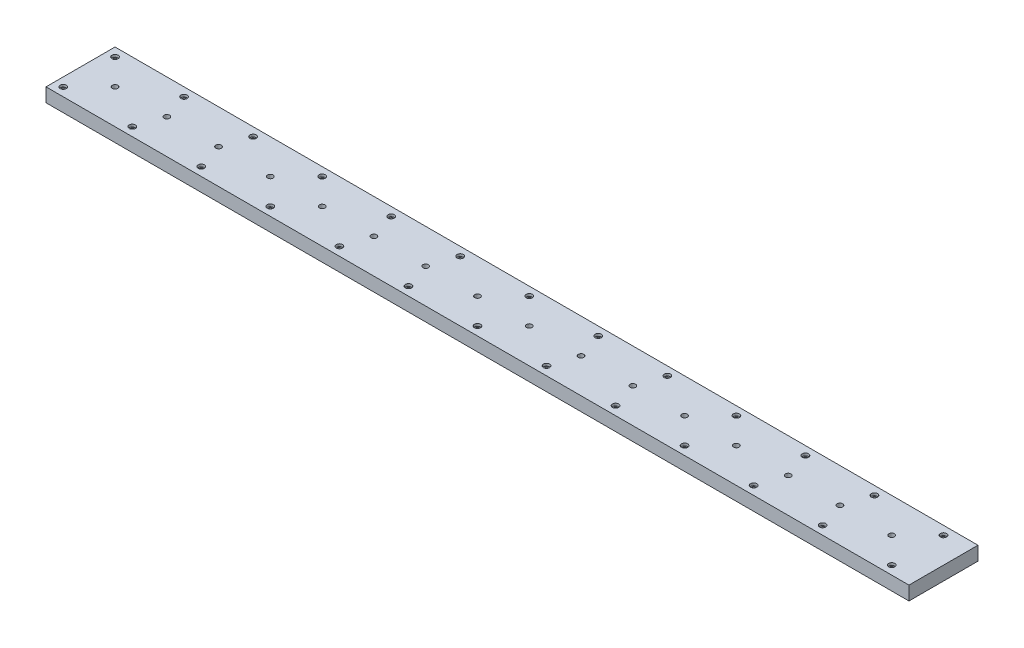
SolidWorks part; units mm, degrees
material "Liga 6061"
ref_plane "Plano frontal" through (0, 0, 0) normal (0, 0, 1) x (1, 0, 0)
ref_plane "Plano superior" through (0, 0, 0) normal (0, 1, 0) x (1, 0, 0)
ref_plane "Plano direito" through (0, 0, 0) normal (1, 0, 0) x (0, 0, -1)
sketch "Esboço1" plane through (0, 0, 0) normal (0, 1, 0) x (1, 0, 0)
  line L1 (-1250, -100) -> (1250, -100)
  line L2 (-1250, -100) -> (-1250, 100)
  line L3 (-1250, 100) -> (1250, 100)
  line L4 (1250, -100) -> (1250, 100)
  line L5 (-1250, -100) -> (1250, 100) construction
  line L6 (-1250, 100) -> (1250, -100) construction
  point P0 (0, 0)
  dimension "D1" = 2500
  dimension "D2" = 200
extrude "Ressalto-extrusão1" add sketch "Esboço1" along normal blind 40
hole_wizard "Rebaixo para parafuso Allen sextavado de M101" positions "Esboço3" profile "Esboço2" counterbore size "M10" standard "DIN" end condition up to next
sketch "Esboço3" plane through (0, 40, 0) normal (0, 1, 0) x (1, 0, 0)
  line L0 (-1250, 100) -> (-1250, -100) construction
  line L1 (1250, 100) -> (-1250, 100) construction
  point P0 (-1225, 75)
  point P12 (-1025, 75)
  point P13 (-825, 75)
  point P14 (-625, 75)
  point P15 (-425, 75)
  point P16 (-225, 75)
  point P17 (-25, 75)
  point P18 (175, 75)
  point P19 (375, 75)
  point P20 (575, 75)
  point P21 (-1025, -75)
  point P22 (-825, -75)
  point P23 (-625, -75)
  point P24 (-425, -75)
  point P25 (-225, -75)
  point P26 (-25, -75)
  point P27 (175, -75)
  point P28 (375, -75)
  point P29 (575, -75)
  point P30 (-1225, -75)
  point P31 (775, 75)
  point P32 (775, -75)
  point P33 (975, 75)
  point P34 (1175, 75)
  point P35 (975, -75)
  point P36 (1175, -75)
  dimension "D1" = 25
  dimension "D2" = 25
  dimension "D3" = 13
  dimension "D4" = 2
sketch "Esboço2" plane through (-1225, 40, -75) normal (1, 0, 0) x (0, 0, 1)
  line L0 (0, 0) -> (0, 40)
  line L1 (0, 40) -> (5.5, 40)
  line L3 (5.5, 40) -> (5.5, 7.1)
  line L4 (5.5, 7.1) -> (9, 7.1)
  line L5 (9, 7.1) -> (9, 0)
  line L7 (9, 0) -> (0, 0)
  line L11 (0, -6.35) -> (0, 107.95) construction
  dimension "Thru Hole Dia." = 11
  dimension "Thru Hole Depth" = 40
  dimension "C'Bore Dia." = 18
  dimension "C'Bore Depth" = 7.1
hole_wizard "Furo roscado de M18x2.0" positions "Esboço7" profile "Esboço6" tap size "M18x2.0" standard "Ansi Metric" end condition up to next
sketch "Esboço7" plane through (0, 40, 0) normal (0, 1, 0) x (1, 0, 0)
  line L0 (-1250, 100) -> (-1250, -100) construction
  line L1 (-1150, 0) -> (-1250, 0) construction
  point P0 (-1150, 0)
  point P5 (-1250, 0)
  point P72 (-1000, 0)
  point P73 (-850, 0)
  point P74 (-700, 0)
  point P75 (-550, 0)
  point P76 (-400, 0)
  point P77 (-250, 0)
  point P78 (-100, 0)
  point P79 (50, 0)
  point P80 (200, 0)
  point P81 (350, 0)
  point P82 (500, 0)
  point P83 (650, 0)
  point P84 (800, 0)
  point P85 (950, 0)
  point P86 (1100, 0)
  dimension "D2" = 100
  dimension "D1" = 16
sketch "Esboço6" plane through (-1150, 40, 0) normal (1, 0, 0) x (0, 0, 1)
  line L0 (0, 0) -> (0, 40)
  line L1 (0, 40) -> (8, 40)
  line L2 (8, 40) -> (8, 0)
  line L5 (8, 0) -> (0, 0)
  line L11 (0, -6.35) -> (0, 107.95) construction
  dimension "Thru Tap Drill Dia." = 16
  dimension "Thru Tap Drill Depth" = 40
cosmetic thread "Rosca de furo5" parameters "D2"=16
cosmetic thread "Rosca de furo6" parameters "D2"=16
cosmetic thread "Rosca de furo7" parameters "D2"=16
cosmetic thread "Rosca de furo8" parameters "D2"=16
cosmetic thread "Rosca de furo9" parameters "D2"=16
cosmetic thread "Rosca de furo10" parameters "D2"=16
cosmetic thread "Rosca de furo11" parameters "D2"=16
cosmetic thread "Rosca de furo12" parameters "D2"=16
cosmetic thread "Rosca de furo13" parameters "D2"=16
cosmetic thread "Rosca de furo14" parameters "D2"=16
cosmetic thread "Rosca de furo15" parameters "D2"=16
cosmetic thread "Rosca de furo16" parameters "D2"=16
cosmetic thread "Rosca de furo17" parameters "D2"=16
cosmetic thread "Rosca de furo18" parameters "D2"=16
cosmetic thread "Rosca de furo37" parameters "D2"=16
cosmetic thread "Rosca de furo38" parameters "D2"=16
hole_wizard "Furo roscado de M16x2.0" [suppressed] positions "Esboço9" profile "Esboço8" tap size "M16x2.0" standard "Ansi Metric"
sketch "Esboço9" plane through (0, 40, 0) normal (0, 1, 0) x (1, 0, 0)
  line L0 (-1020, 0) -> (-1050, 0) construction
  line L1 (-1050, 100) -> (-1050, -100) construction
  line L2 (1020, 0) -> (1050, 0) construction
  line L3 (1050, -100) -> (1050, 100) construction
  point P0 (-1020, 0)
  point P13 (-900, 0)
  point P14 (-780, 0)
  point P15 (-660, 0)
  point P16 (-540, 0)
  point P17 (-420, 0)
  point P18 (-300, 0)
  point P19 (-180, 0)
  point P20 (-60, 0)
  point P21 (60, 0)
  point P22 (180, 0)
  point P23 (300, 0)
  point P24 (420, 0)
  point P25 (540, 0)
  point P26 (660, 0)
  point P27 (780, 0)
  point P28 (900, 0)
  point P29 (1020, 0)
  dimension "D1" = 18
sketch "Esboço8" plane through (-1020, 40, 0) normal (1, 0, 0) x (0, 0, 1)
  line L0 (0, 0) -> (0, 40)
  line L1 (0, 40) -> (7, 40)
  line L2 (7, 40) -> (7, 0)
  line L5 (7, 0) -> (0, 0)
  line L11 (0, -6.35) -> (0, 107.95) construction
  dimension "Thru Tap Drill Dia." = 14
  dimension "Thru Tap Drill Depth" = 40
cosmetic thread "Rosca de furo19" [suppressed] parameters "D2"=16
cosmetic thread "Rosca de furo20" [suppressed] parameters "D2"=16
cosmetic thread "Rosca de furo21" [suppressed] parameters "D2"=16
cosmetic thread "Rosca de furo22" [suppressed] parameters "D2"=16
cosmetic thread "Rosca de furo23" [suppressed] parameters "D2"=16
cosmetic thread "Rosca de furo24" [suppressed] parameters "D2"=16
cosmetic thread "Rosca de furo25" [suppressed] parameters "D2"=16
cosmetic thread "Rosca de furo26" [suppressed] parameters "D2"=16
cosmetic thread "Rosca de furo27" [suppressed] parameters "D2"=16
cosmetic thread "Rosca de furo28" [suppressed] parameters "D2"=16
cosmetic thread "Rosca de furo29" [suppressed] parameters "D2"=16
cosmetic thread "Rosca de furo30" [suppressed] parameters "D2"=16
cosmetic thread "Rosca de furo31" [suppressed] parameters "D2"=16
cosmetic thread "Rosca de furo32" [suppressed] parameters "D2"=16
cosmetic thread "Rosca de furo33" [suppressed] parameters "D2"=16
cosmetic thread "Rosca de furo34" [suppressed] parameters "D2"=16
cosmetic thread "Rosca de furo35" [suppressed] parameters "D2"=16
cosmetic thread "Rosca de furo36" [suppressed] parameters "D2"=16
